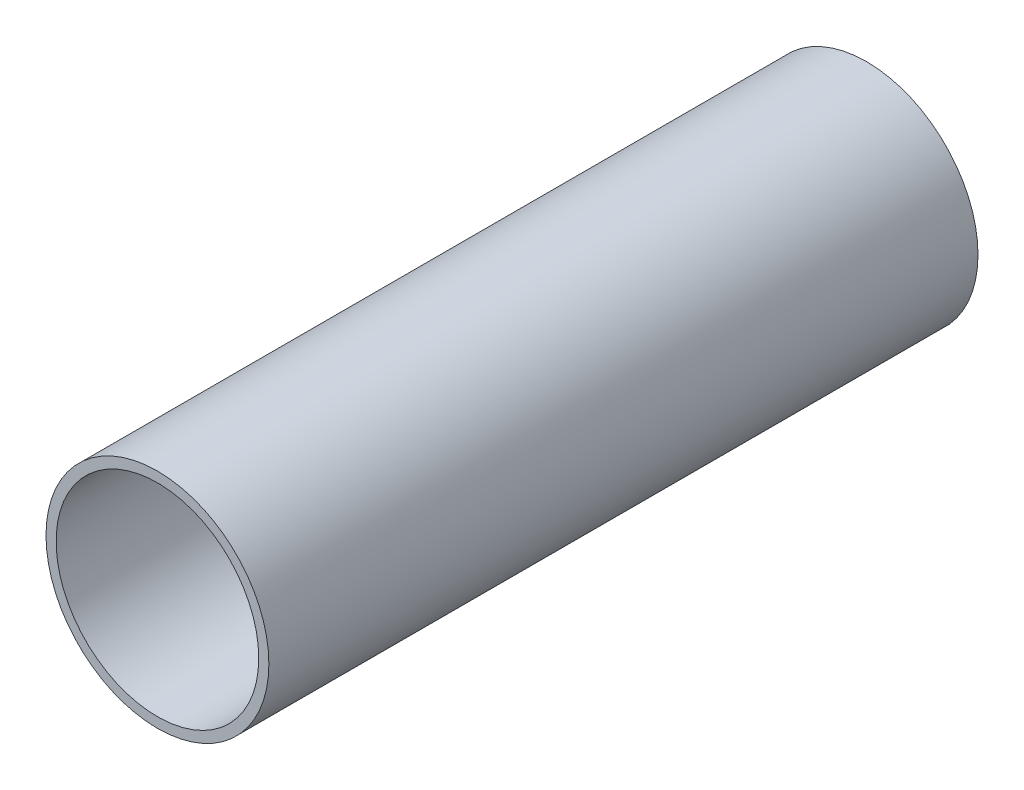
SolidWorks part; units mm, degrees
material "Сплав 2024"
ref_plane "Спереди" through (0, 0, 0) normal (0, 0, 1) x (1, 0, 0)
ref_plane "Сверху" through (0, 0, 0) normal (0, 1, 0) x (1, 0, 0)
ref_plane "Справа" through (0, 0, 0) normal (1, 0, 0) x (0, 0, -1)
sketch "Эскиз1" plane through (0, 0, 0) normal (0, 0, 1) x (1, 0, 0)
  circle A0 centre (0, 0) radius 11
  circle A1 centre (0, 0) radius 10
  dimension "D1" = 22
  dimension "D2" = 1
extrude "Бобышка-Вытянуть1" add sketch "Эскиз1" along normal blind 70
